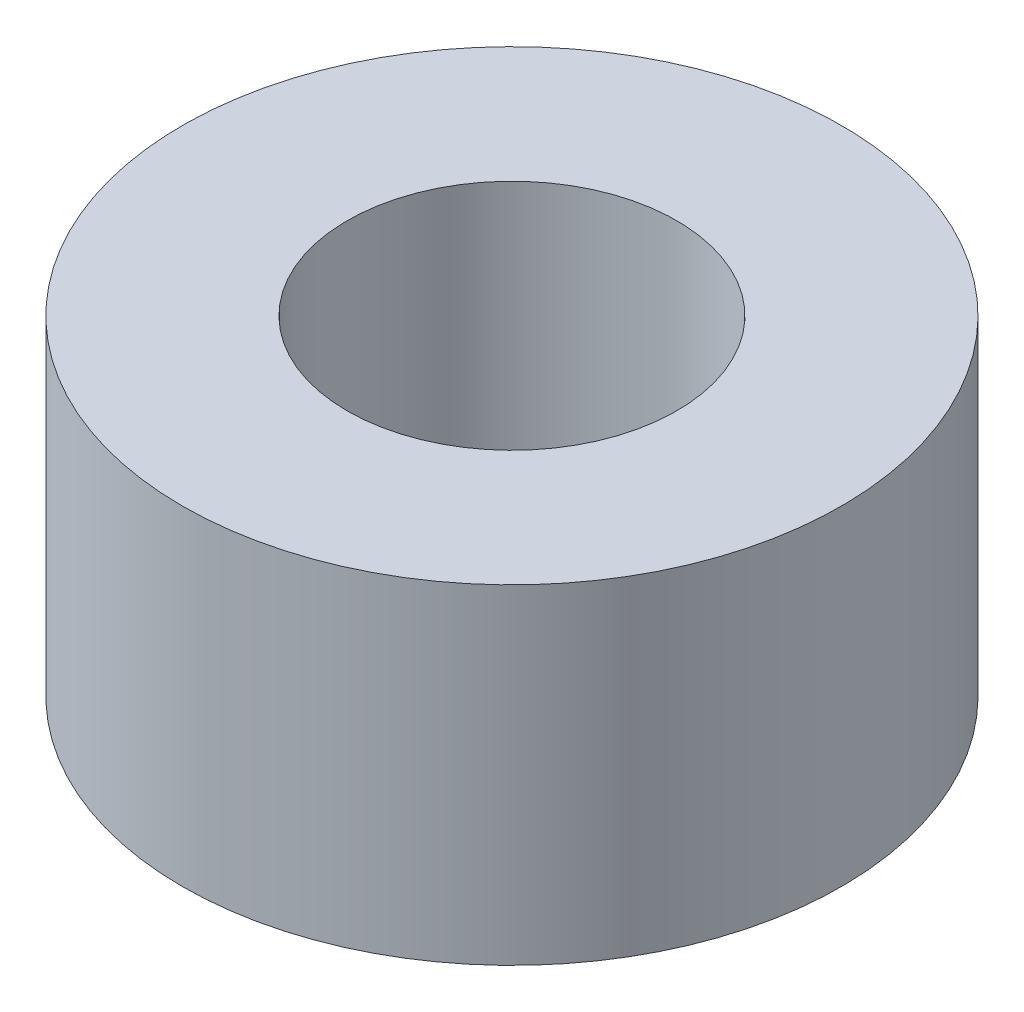
SolidWorks part; units mm, degrees
ref_plane "Front Plane" through (0, 0, 0) normal (0, 0, 1) x (1, 0, 0)
ref_plane "Top Plane" through (0, 0, 0) normal (0, 1, 0) x (1, 0, 0)
ref_plane "Right Plane" through (0, 0, 0) normal (1, 0, 0) x (0, 0, -1)
sketch "Sketch2" plane through (0, 0, 0) normal (0, 1, 0) x (1, 0, 0)
  circle A1 centre (0, 0) radius 6.35
  dimension "D1" = 12.7
extrude "Boss-Extrude1" add sketch "Sketch2" along normal blind 6.35
hole_wizard "1/4-20 Tapped Hole1" positions "Sketch4" profile "Sketch3" tap size "1/4-20" standard "ANSI Inch" end condition through all
sketch "Sketch4" plane through (0, 6.35, 0) normal (0, 1, 0) x (1, 0, 0)
  point P0 (0, 0)
sketch "Sketch3" plane through (0, 6.35, 0) normal (1, 0, 0) x (0, 0, 1)
  line L0 (0, 0) -> (0, 6.35)
  line L1 (0, 6.35) -> (3.175, 6.35)
  line L2 (3.175, 6.35) -> (3.175, 0)
  line L5 (3.175, 0) -> (0, 0)
  line L11 (0, -6.35) -> (0, 107.95) construction
  dimension "Thread Major Dia." = 6.35
  dimension "Thru Tap Drill Depth" = 6.35
